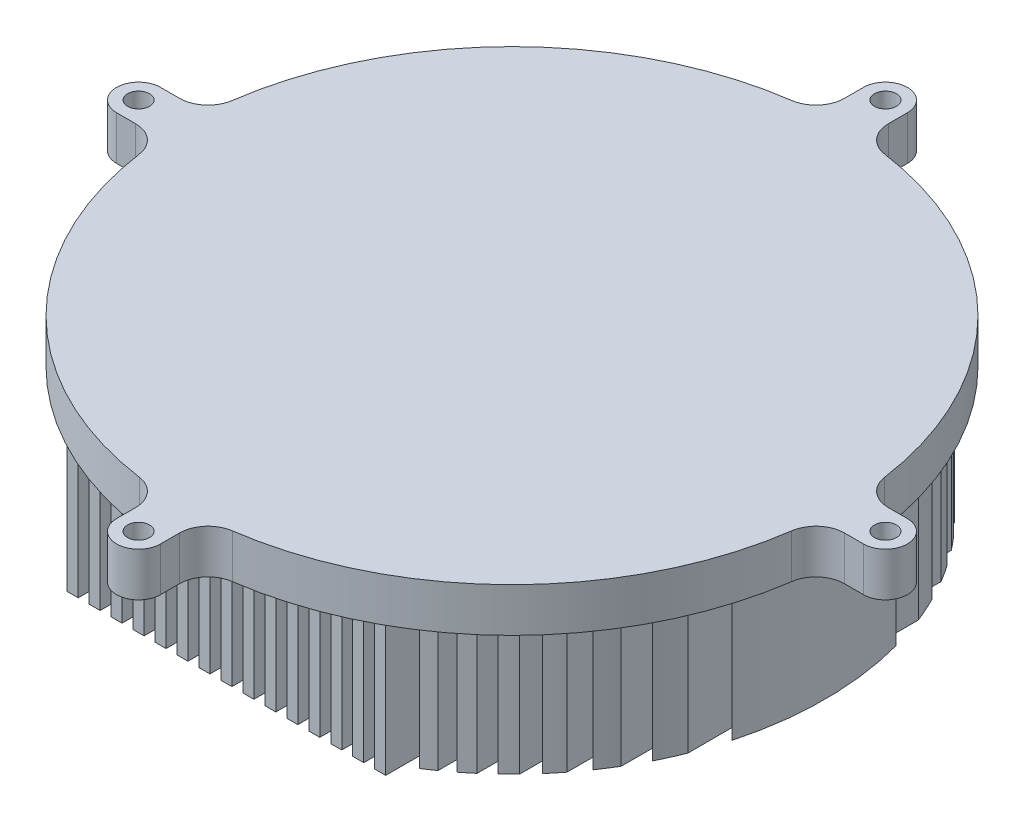
SolidWorks part; units mm, degrees
ref_plane "Front Plane" through (0, 0, 0) normal (0, 0, 1) x (1, 0, 0)
ref_plane "Top Plane" through (0, 0, 0) normal (0, 1, 0) x (1, 0, 0)
ref_plane "Right Plane" through (0, 0, 0) normal (1, 0, 0) x (0, 0, -1)
sketch "Sketch3" plane through (0, 0, 0) normal (0, 1, 0) x (1, 0, 0)
  line L0 (0, 0) -> (211.9111, 0) construction
  line L1 (0, 0) -> (-205.2426, 0) construction
  line L2 (0, 0) -> (0, 170) construction
  line L3 (0, 0) -> (0, -200) construction
  line L4 (161.3691, 10) -> (170, 10)
  line L5 (161.3691, -10) -> (170, -10)
  line L6 (-10, 161.3691) -> (-10, 170)
  line L7 (10, 161.3691) -> (10, 170)
  line L8 (10, -161.3691) -> (10, -170)
  line L9 (-10, -161.3691) -> (-10, -170)
  line L10 (-161.3691, -10) -> (-170, -10)
  line L11 (-161.3691, 10) -> (-170, 10)
  arc A0 (-21.1656, 148.4992) -> (-148.4992, 21.1656) centre (0, 0) ccw
  circle A1 centre (0, 170) radius 5
  arc A2 (-10, 170) -> (10, 170) centre (0, 170) cw
  arc A3 (10, 161.3691) -> (21.1656, 148.4992) centre (23, 161.3691) ccw
  arc A4 (-10, 161.3691) -> (-21.1656, 148.4992) centre (-23, 161.3691) cw
  arc A5 (170, 10) -> (170, -10) centre (170, 0) cw
  arc A6 (161.3691, 10) -> (148.4992, 21.1656) centre (161.3691, 23) cw
  circle A7 centre (170, 0) radius 5
  arc A8 (161.3691, -10) -> (148.4992, -21.1656) centre (161.3691, -23) ccw
  arc A9 (10, -170) -> (-10, -170) centre (0, -170) cw
  arc A10 (10, -161.3691) -> (21.1656, -148.4992) centre (23, -161.3691) cw
  circle A11 centre (0, -170) radius 5
  arc A12 (-10, -161.3691) -> (-21.1656, -148.4992) centre (-23, -161.3691) ccw
  arc A13 (-170, -10) -> (-170, 10) centre (-170, 0) cw
  arc A14 (-161.3691, -10) -> (-148.4992, -21.1656) centre (-161.3691, -23) cw
  circle A15 centre (-170, 0) radius 5
  arc A16 (-161.3691, 10) -> (-148.4992, 21.1656) centre (-161.3691, 23) ccw
  arc A17 (-148.4992, -21.1656) -> (-21.1656, -148.4992) centre (0, 0) ccw
  arc A18 (148.4992, 21.1656) -> (21.1656, 148.4992) centre (0, 0) ccw
  arc A19 (21.1656, -148.4992) -> (148.4992, -21.1656) centre (0, 0) ccw
  point P53 (0, 0)
  dimension "D1" = 300
  dimension "D4" = 10
  dimension "D2" = 4
extrude "Boss-Extrude4" add sketch "Sketch3" against normal blind 20
sketch "Sketch4" plane through (0, -20, 0) normal (0, 1, 0) x (1, 0, 0)
  line L0 (0, 0) -> (0, 214.2399) construction
  line L1 (0, 0) -> (0, -238.4864) construction
  line L2 (0, 0) -> (-208.9775, 0) construction
  line L3 (0, 0) -> (218.7408, 0) construction
  line L4 (2.5, 130) -> (-2.5, 130)
  line L5 (-2.5, 130) -> (-2.5, -130)
  line L6 (2.5, 130) -> (2.5, -130)
  line L7 (2.5, -130) -> (-2.5, -130)
  line L8 (12.5, 130) -> (12.5, -130)
  line L9 (12.5, 130) -> (7.5, 130)
  line L10 (7.5, 130) -> (7.5, -130)
  line L11 (12.5, -130) -> (7.5, -130)
  line L12 (22.5, 130) -> (22.5, -130)
  line L13 (22.5, 130) -> (17.5, 130)
  line L14 (17.5, 130) -> (17.5, -130)
  line L15 (22.5, -130) -> (17.5, -130)
  line L16 (32.5, 130) -> (32.5, -130)
  line L17 (32.5, 130) -> (27.5, 130)
  line L18 (27.5, 130) -> (27.5, -130)
  line L19 (32.5, -130) -> (27.5, -130)
  line L20 (42.5, 130) -> (42.5, -130)
  line L21 (42.5, 130) -> (37.5, 130)
  line L22 (37.5, 130) -> (37.5, -130)
  line L23 (42.5, -130) -> (37.5, -130)
  line L24 (52.5, 130) -> (52.5, -130)
  line L25 (52.5, 130) -> (47.5, 130)
  line L26 (47.5, 130) -> (47.5, -130)
  line L27 (52.5, -130) -> (47.5, -130)
  line L28 (62.5, 130) -> (62.5, -130)
  line L29 (62.5, 130) -> (57.5, 130)
  line L30 (57.5, 130) -> (57.5, -130)
  line L31 (62.5, -130) -> (57.5, -130)
  line L32 (72.5, 130) -> (72.5, -130)
  line L33 (72.5, 130) -> (67.5, 130)
  line L34 (67.5, 130) -> (67.5, -130)
  line L35 (72.5, -130) -> (67.5, -130)
  line L36 (82.5, 116.1895) -> (82.5, -116.1895)
  line L38 (77.5, 119.5826) -> (77.5, -119.5826)
  line L40 (92.5, 108.3974) -> (92.5, -108.3974)
  line L42 (87.5, 112.4722) -> (87.5, -112.4722)
  line L44 (102.5, 98.9949) -> (102.5, -98.9949)
  line L46 (97.5, 103.923) -> (97.5, -103.923)
  line L48 (112.5, 87.4643) -> (112.5, -87.4643)
  line L50 (107.5, 93.5414) -> (107.5, -93.5414)
  line L52 (-7.5, 130) -> (-12.5, 130)
  line L53 (-12.5, 130) -> (-12.5, -130)
  line L54 (-7.5, 130) -> (-7.5, -130)
  line L55 (-7.5, -130) -> (-12.5, -130)
  line L56 (-17.5, 130) -> (-22.5, 130)
  line L57 (-22.5, 130) -> (-22.5, -130)
  line L58 (-17.5, 130) -> (-17.5, -130)
  line L59 (-17.5, -130) -> (-22.5, -130)
  line L60 (-27.5, 130) -> (-32.5, 130)
  line L61 (-32.5, 130) -> (-32.5, -130)
  line L62 (-27.5, 130) -> (-27.5, -130)
  line L63 (-27.5, -130) -> (-32.5, -130)
  line L64 (-37.5, 130) -> (-42.5, 130)
  line L65 (-42.5, 130) -> (-42.5, -130)
  line L66 (-37.5, 130) -> (-37.5, -130)
  line L67 (-37.5, -130) -> (-42.5, -130)
  line L68 (-47.5, 130) -> (-52.5, 130)
  line L69 (-52.5, 130) -> (-52.5, -130)
  line L70 (-47.5, 130) -> (-47.5, -130)
  line L71 (-47.5, -130) -> (-52.5, -130)
  line L72 (-57.5, 130) -> (-62.5, 130)
  line L73 (-62.5, 130) -> (-62.5, -130)
  line L74 (-57.5, 130) -> (-57.5, -130)
  line L75 (-57.5, -130) -> (-62.5, -130)
  line L76 (-67.5, 130) -> (-72.5, 130)
  line L77 (-72.5, 130) -> (-72.5, -130)
  line L78 (-67.5, 130) -> (-67.5, -130)
  line L79 (-67.5, -130) -> (-72.5, -130)
  line L81 (-82.5, 116.1895) -> (-82.5, -116.1895)
  line L82 (-77.5, 119.5826) -> (-77.5, -119.5826)
  line L85 (-92.5, 108.3974) -> (-92.5, -108.3974)
  line L86 (-87.5, 112.4722) -> (-87.5, -112.4722)
  line L89 (-102.5, 98.9949) -> (-102.5, -98.9949)
  line L90 (-97.5, 103.923) -> (-97.5, -103.923)
  line L93 (-112.5, 87.4643) -> (-112.5, -87.4643)
  line L94 (-107.5, 93.5414) -> (-107.5, -93.5414)
  line L97 (-122.5, 72.8011) -> (-122.5, -72.8011)
  line L98 (-117.5, 80.6226) -> (-117.5, -80.6226)
  line L101 (-132.5, 52.4404) -> (-132.5, -52.4404)
  line L102 (-127.5, 63.6396) -> (-127.5, -63.6396)
  line L106 (-137.5, 37.4166) -> (-137.5, -37.4166)
  line L108 (122.5, 72.8011) -> (122.5, -72.8011)
  line L110 (117.5, 80.6226) -> (117.5, -80.6226)
  line L112 (132.5, 52.4404) -> (132.5, -52.4404)
  line L114 (127.5, 63.6396) -> (127.5, -63.6396)
  line L118 (137.5, 37.4166) -> (137.5, -37.4166)
  line L120 (-142.5, 130) -> (-142.5, -130) [skipped]
  line L121 (142.5, 0) -> (142.5, -130) [skipped]
  line L122 (-77.5, -130) -> (-82.5, -130) [skipped]
  line L123 (-87.5, -130) -> (-92.5, -130) [skipped]
  line L124 (-97.5, -130) -> (-102.5, -130) [skipped]
  line L125 (-107.5, -130) -> (-112.5, -130) [skipped]
  line L126 (-117.5, -130) -> (-122.5, -130) [skipped]
  line L127 (-127.5, -130) -> (-132.5, -130) [skipped]
  line L128 (-137.5, -130) -> (-142.5, -130) [skipped]
  line L129 (92.5, -130) -> (87.5, -130) [skipped]
  line L130 (102.5, -130) -> (97.5, -130) [skipped]
  line L131 (112.5, -130) -> (107.5, -130) [skipped]
  line L132 (122.5, -130) -> (117.5, -130) [skipped]
  line L133 (132.5, -130) -> (127.5, -130) [skipped]
  line L134 (142.5, -130) -> (137.5, -130) [skipped]
  line L135 (82.5, -130) -> (77.5, -130) [skipped]
  line L136 (92.5, 130) -> (87.5, 130) [skipped]
  line L137 (102.5, 130) -> (97.5, 130) [skipped]
  line L138 (112.5, 130) -> (107.5, 130) [skipped]
  line L139 (122.5, 130) -> (117.5, 130) [skipped]
  line L140 (132.5, 130) -> (127.5, 130) [skipped]
  line L141 (142.5, 130) -> (137.5, 130) [skipped]
  line L142 (82.5, 130) -> (77.5, 130) [skipped]
  line L143 (-77.5, 130) -> (-82.5, 130) [skipped]
  line L144 (-87.5, 130) -> (-92.5, 130) [skipped]
  line L145 (-97.5, 130) -> (-102.5, 130) [skipped]
  line L146 (-107.5, 130) -> (-112.5, 130) [skipped]
  line L147 (-117.5, 130) -> (-122.5, 130) [skipped]
  line L148 (-127.5, 130) -> (-132.5, 130) [skipped]
  line L149 (-137.5, 130) -> (-142.5, 130) [skipped]
  arc A0 (-137.5, 37.4166) -> (-137.5, -37.4166) centre (0, 0) ccw
  arc A1 (-127.5, 63.6396) -> (-132.5, 52.4404) centre (0, 0) ccw
  arc A2 (-117.5, 80.6226) -> (-122.5, 72.8011) centre (0, 0) ccw
  arc A3 (-132.5, -52.4404) -> (-127.5, -63.6396) centre (0, 0) ccw
  arc A4 (-122.5, -72.8011) -> (-117.5, -80.6226) centre (0, 0) ccw
  arc A5 (-112.5, -87.4643) -> (-107.5, -93.5414) centre (0, 0) ccw
  arc A6 (-102.5, -98.9949) -> (-97.5, -103.923) centre (0, 0) ccw
  arc A7 (132.5, 52.4404) -> (127.5, 63.6396) centre (0, 0) ccw
  arc A8 (122.5, 72.8011) -> (117.5, 80.6226) centre (0, 0) ccw
  arc A9 (112.5, 87.4643) -> (107.5, 93.5414) centre (0, 0) ccw
  arc A10 (102.5, 98.9949) -> (97.5, 103.923) centre (0, 0) ccw
  arc A11 (92.5, 108.3974) -> (87.5, 112.4722) centre (0, 0) ccw
  arc A12 (82.5, 116.1895) -> (77.5, 119.5826) centre (0, 0) ccw
  arc A13 (-77.5, 119.5826) -> (-82.5, 116.1895) centre (0, 0) ccw
  arc A15 (-87.5, 112.4722) -> (-92.5, 108.3974) centre (0, 0) ccw
  arc A16 (-97.5, 103.923) -> (-102.5, 98.9949) centre (0, 0) ccw
  arc A17 (-107.5, 93.5414) -> (-112.5, 87.4643) centre (0, 0) ccw
  arc A19 (-82.5, -116.1895) -> (-77.5, -119.5826) centre (0, 0) ccw
  arc A20 (-92.5, -108.3974) -> (-87.5, -112.4722) centre (0, 0) ccw
  arc A21 (137.5, -37.4166) -> (137.5, 37.4166) centre (0, 0) ccw
  arc A22 (127.5, -63.6396) -> (132.5, -52.4404) centre (0, 0) ccw
  arc A23 (117.5, -80.6226) -> (122.5, -72.8011) centre (0, 0) ccw
  arc A24 (107.5, -93.5414) -> (112.5, -87.4643) centre (0, 0) ccw
  arc A25 (97.5, -103.923) -> (102.5, -98.9949) centre (0, 0) ccw
  arc A26 (87.5, -112.4722) -> (92.5, -108.3974) centre (0, 0) ccw
  arc A27 (77.5, -119.5826) -> (82.5, -116.1895) centre (0, 0) ccw
  dimension "D1" = 130
  dimension "D2" = 2.5
  dimension "D3" = 2.5
  dimension "D4" = 130
  dimension "D5" = 15
  dimension "D6" = 15
extrude "Boss-Extrude5" add sketch "Sketch4" against normal blind 60
